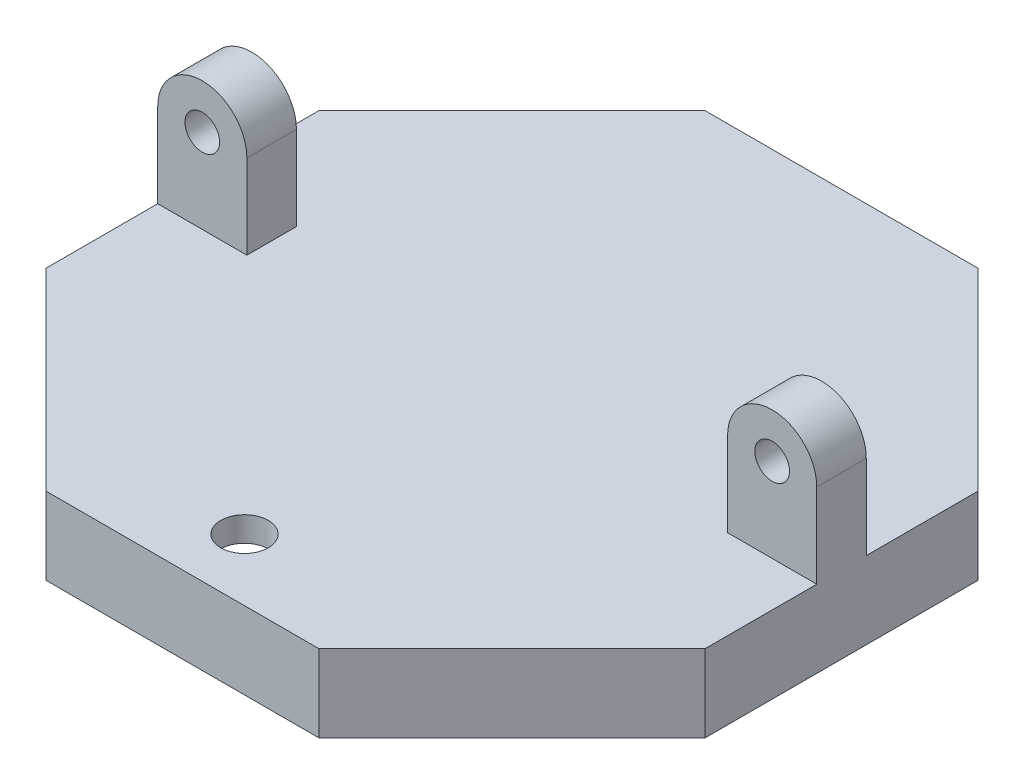
SolidWorks part; units mm, degrees
ref_plane "정면" through (0, 0, 0) normal (0, 0, 1) x (1, 0, 0)
ref_plane "윗면" through (0, 0, 0) normal (0, 1, 0) x (1, 0, 0)
ref_plane "우측면" through (0, 0, 0) normal (1, 0, 0) x (0, 0, -1)
sketch "스케치1" plane through (0, 0, 0) normal (0, 1, 0) x (1, 0, 0)
  line L0 (-55, 0) -> (55, 0) construction
  line L1 (-32.0597, 13.2795) -> (-32.0597, -13.2795)
  line L2 (-32.0597, -13.2795) -> (-13.2795, -32.0597)
  line L3 (-13.2795, -32.0597) -> (13.2795, -32.0597)
  line L4 (13.2795, -32.0597) -> (32.0597, -13.2795)
  line L5 (32.0597, -13.2795) -> (32.0597, 13.2795)
  line L6 (32.0597, 13.2795) -> (13.2795, 32.0597)
  line L7 (13.2795, 32.0597) -> (-13.2795, 32.0597)
  line L8 (-13.2795, 32.0597) -> (-32.0597, 13.2795)
  line L9 (-33.2597, 13.7766) -> (-33.2597, -13.7766)
  line L10 (-33.2597, -13.7766) -> (-13.7766, -33.2597)
  line L11 (-13.7766, -33.2597) -> (13.7766, -33.2597)
  line L12 (13.7766, -33.2597) -> (33.2597, -13.7766)
  line L13 (33.2597, -13.7766) -> (33.2597, 13.7766)
  line L14 (33.2597, 13.7766) -> (13.7766, 33.2597)
  line L15 (13.7766, 33.2597) -> (-13.7766, 33.2597)
  line L16 (-13.7766, 33.2597) -> (-33.2597, 13.7766)
  circle A0 centre (0, 0) radius 34.7011 construction
  dimension "D1" = 72
  dimension "D2" = 1.2
extrude "보스-돌출1" add sketch "스케치1" along normal blind 2.5 contours L7 L8 L1 L2 L3 L4 L5 L6 | L15 L16 L9 L10 L11 L12 L13 L14 L8 L7 L6 L5 L4 L3 L2 L1
sketch "스케치2" plane through (0, 0, 0) normal (0, -1, 0) x (1, 0, 0)
  line L8 (-12.7825, -30.8597) -> (12.7825, -30.8597)
  line L9 (12.7825, -30.8597) -> (30.8597, -12.7825)
  line L10 (30.8597, -12.7825) -> (30.8597, 12.7825)
  line L11 (30.8597, 12.7825) -> (12.7825, 30.8597)
  line L12 (12.7825, 30.8597) -> (-12.7825, 30.8597)
  line L13 (-12.7825, 30.8597) -> (-30.8597, 12.7825)
  line L14 (-30.8597, 12.7825) -> (-30.8597, -12.7825)
  line L15 (-30.8597, -12.7825) -> (-12.7825, -30.8597)
  line L16 (-13.2795, -32.0597) -> (13.2795, -32.0597)
  line L17 (13.2795, -32.0597) -> (32.0597, -13.2795)
  line L18 (32.0597, -13.2795) -> (32.0597, 13.2795)
  line L19 (32.0597, 13.2795) -> (13.2795, 32.0597)
  line L20 (13.2795, 32.0597) -> (-13.2795, 32.0597)
  line L21 (-13.2795, 32.0597) -> (-32.0597, 13.2795)
  line L22 (-32.0597, 13.2795) -> (-32.0597, -13.2795)
  line L23 (-32.0597, -13.2795) -> (-13.2795, -32.0597)
  line L24 (-13.2795, -32.0597) -> (13.2795, -32.0597)
  line L25 (13.2795, -32.0597) -> (32.0597, -13.2795)
  line L26 (32.0597, -13.2795) -> (32.0597, 13.2795)
  line L27 (32.0597, 13.2795) -> (13.2795, 32.0597)
  line L28 (13.2795, 32.0597) -> (-13.2795, 32.0597)
  line L29 (-13.2795, 32.0597) -> (-32.0597, 13.2795)
  line L30 (-32.0597, 13.2795) -> (-32.0597, -13.2795)
  line L31 (-32.0597, -13.2795) -> (-13.2795, -32.0597)
  line L32 (-12.2854, -29.6597) -> (12.2854, -29.6597)
  line L33 (12.2854, -29.6597) -> (29.6597, -12.2854)
  line L34 (29.6597, -12.2854) -> (29.6597, 12.2854)
  line L35 (29.6597, 12.2854) -> (12.2854, 29.6597)
  line L36 (12.2854, 29.6597) -> (-12.2854, 29.6597)
  line L37 (-12.2854, 29.6597) -> (-29.6597, 12.2854)
  line L38 (-29.6597, 12.2854) -> (-29.6597, -12.2854)
  line L39 (-29.6597, -12.2854) -> (-12.2854, -29.6597)
  line M17 (-13.7766, -33.2597) -> (13.7766, -33.2597)
  line M18 (13.7766, -33.2597) -> (33.2597, -13.7766)
  line M19 (33.2597, -13.7766) -> (33.2597, 13.7766)
  line M20 (33.2597, 13.7766) -> (13.7766, 33.2597)
  line M21 (13.7766, 33.2597) -> (-13.7766, 33.2597)
  line M22 (-13.7766, 33.2597) -> (-33.2597, 13.7766)
  line M23 (-33.2597, 13.7766) -> (-33.2597, -13.7766)
  line M24 (-33.2597, -13.7766) -> (-13.7766, -33.2597)
  dimension "D1" = 1.2
  dimension "D2" = 1.2
  dimension "D3" = 1.2
extrude "보스-돌출2" add sketch "스케치2" along normal blind 5.3 contours L31 L30 L29 L28 L27 L26 L25 L24 M24 M17 M18 M19 M20 M21 M22 M23 | L30 L31 L24 L25 L26 L27 L28 L29 L15 L14 L13 L12 L11 L10 L9 L8 | L14 L15 L8 L9 L10 L11 L12 L13 L39 L38 L37 L36 L35 L34 L33 L32
sketch "스케치3" plane through (0, -5.3, 0) normal (0, -1, 0) x (1, 0, 0)
  line L8 (-30.8597, -12.7825) -> (-12.7825, -30.8597)
  line L9 (-12.7825, -30.8597) -> (12.7825, -30.8597)
  line L10 (12.7825, -30.8597) -> (30.8597, -12.7825)
  line L11 (30.8597, -12.7825) -> (30.8597, 12.7825)
  line L12 (30.8597, 12.7825) -> (12.7825, 30.8597)
  line L13 (12.7825, 30.8597) -> (-12.7825, 30.8597)
  line L14 (-12.7825, 30.8597) -> (-30.8597, 12.7825)
  line L15 (-30.8597, 12.7825) -> (-30.8597, -12.7825)
  line L16 (-32.0597, -13.2795) -> (-13.2795, -32.0597)
  line L17 (-13.2795, -32.0597) -> (13.2795, -32.0597)
  line L18 (13.2795, -32.0597) -> (32.0597, -13.2795)
  line L19 (32.0597, -13.2795) -> (32.0597, 13.2795)
  line L20 (32.0597, 13.2795) -> (13.2795, 32.0597)
  line L21 (13.2795, 32.0597) -> (-13.2795, 32.0597)
  line L22 (-13.2795, 32.0597) -> (-32.0597, 13.2795)
  line L23 (-32.0597, 13.2795) -> (-32.0597, -13.2795)
  line L24 (-32.0597, -13.2795) -> (-13.2795, -32.0597)
  line L25 (-13.2795, -32.0597) -> (13.2795, -32.0597)
  line L26 (13.2795, -32.0597) -> (32.0597, -13.2795)
  line L27 (32.0597, -13.2795) -> (32.0597, 13.2795)
  line L28 (32.0597, 13.2795) -> (13.2795, 32.0597)
  line L29 (13.2795, 32.0597) -> (-13.2795, 32.0597)
  line L30 (-13.2795, 32.0597) -> (-32.0597, 13.2795)
  line L31 (-32.0597, 13.2795) -> (-32.0597, -13.2795)
  dimension "D1" = 1.2
  dimension "D2" = 1.2
extrude "컷-돌출1" cut sketch "스케치3" against normal blind 1
sketch "스케치6" plane through (0, 0, 0) normal (0, -1, 0) x (1, 0, 0)
  circle A4 centre (0, 0) radius 4.015
  dimension "D1" = 8.03
extrude "보스-돌출4" add sketch "스케치6" along normal blind 4
sketch "스케치7" plane through (0, 2.5, 0) normal (0, 1, 0) x (1, 0, 0)
  line L1 (0, -11.44) -> (0, 11.44) construction
  circle A0 centre (0, -27) radius 2.4
  dimension "D1" = 4.8
  dimension "D2" = 27
extrude "컷-돌출3" cut sketch "스케치7" against normal through all
sketch "스케치8" plane through (0, 2.5, 0) normal (0, 1, 0) x (1, 0, 0)
  line L0 (-33.2597, 13.7766) -> (-33.2597, -13.7766) construction
  line L1 (-33.2597, 2.5) -> (-24.2597, 2.5)
  line L2 (-33.2597, 2.5) -> (-33.2597, -2.5)
  line L3 (-33.2597, -2.5) -> (-24.2597, -2.5)
  line L4 (-24.2597, 2.5) -> (-24.2597, -2.5)
  dimension "D2" = 9
  dimension "D3" = 5
  dimension "D4" = 2.5
extrude "보스-돌출5" add sketch "스케치8" along normal blind 8.5
sketch "스케치9" plane through (0, 11, 0) normal (0, 1, 0) x (1, 0, 0)
  line L0 (-28.7597, 5.5088) -> (-28.7597, -6.7586) construction
  line L1 (-33.2597, 2.5) -> (-33.2597, -2.5) construction
  line L6 (-33.2597, 2.5) -> (-33.2597, -2.5)
  line L7 (-33.2597, -2.5) -> (-24.2597, -2.5)
  line L8 (-24.2597, -2.5) -> (-24.2597, 2.5)
  line L9 (-24.2597, 2.5) -> (-33.2597, 2.5)
  line L10 (-33.2597, 2.5) -> (-33.2597, -2.5)
  line L11 (-33.2597, -2.5) -> (-24.2597, -2.5)
  line L12 (-24.2597, -2.5) -> (-24.2597, 2.5)
  line L13 (-24.2597, 2.5) -> (-33.2597, 2.5)
  dimension "D1" = 4.5
  dimension "D2" = 0
revolve "회전1" add sketch "스케치9" angle 360 about L0
sketch "스케치10" plane through (0, 0, 2.5) normal (0, 0, 1) x (1, 0, 0)
  circle A0 centre (-28.7597, 11) radius 1.75
  arc A4 (-24.2597, 11) -> (-33.2597, 11) centre (-28.7597, 11) ccw construction
  dimension "D1" = 3.5
extrude "컷-돌출4" cut sketch "스케치10" against normal through all
mirror "대칭 복사1" about plane through (0, 0, 0) normal (1, 0, 0) of "컷-돌출4", "회전1", "보스-돌출5"
